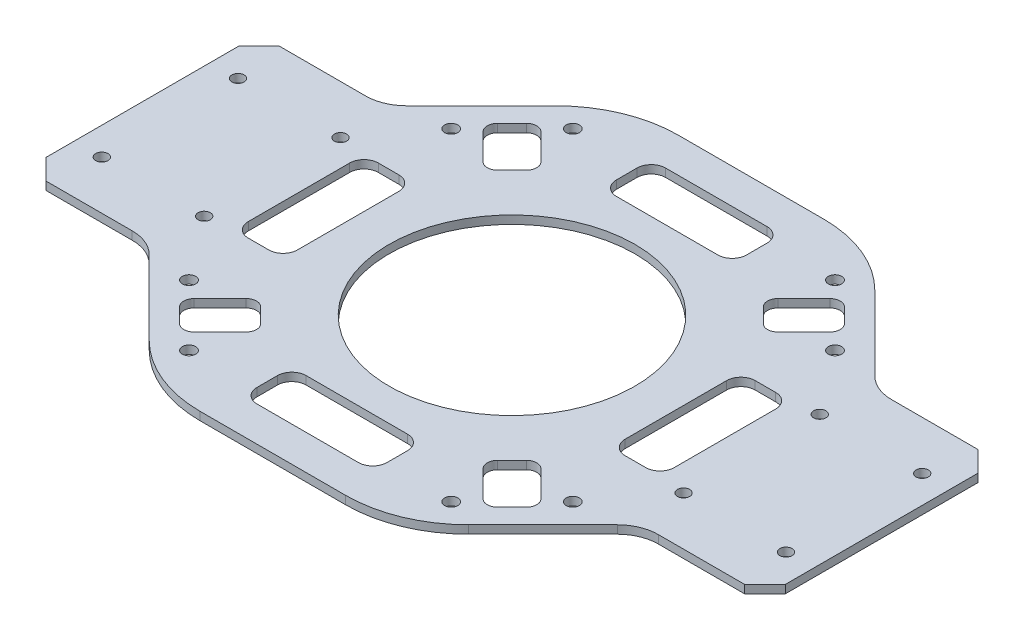
SolidWorks part; units mm, degrees
ref_plane "Front Plane" through (0, 0, 0) normal (0, 0, 1) x (1, 0, 0)
ref_plane "Top Plane" through (0, 0, 0) normal (0, 1, 0) x (1, 0, 0)
ref_plane "Right Plane" through (0, 0, 0) normal (1, 0, 0) x (0, 0, -1)
ref_plane "Plane1" through (0, 3.76, 0) normal (0, 1, 0) x (1, 0, 0)
sketch "Sketch1" plane through (0, 3.76, 0) normal (0, 1, 0) x (1, 0, 0)
  line L0 (-15.875, -46.375) -> (-15.875, -41.375)
  line L1 (-12.375, -37.875) -> (12.375, -37.875)
  line L2 (15.875, -41.375) -> (15.875, -46.375)
  line L3 (12.375, -49.875) -> (-12.375, -49.875)
  line L4 (15.875, 46.375) -> (15.875, 41.375)
  line L5 (12.375, 37.875) -> (-12.375, 37.875)
  line L6 (-15.875, 41.375) -> (-15.875, 46.375)
  line L7 (-12.375, 49.875) -> (12.375, 49.875)
  line L8 (-43.5, -15.875) -> (-48.5, -15.875)
  line L9 (-52, -12.375) -> (-52, 12.375)
  line L10 (-48.5, 15.875) -> (-43.5, 15.875)
  line L11 (-40, 12.375) -> (-40, -12.375)
  line L12 (-32.4385, -28.903) -> (-28.903, -32.4385)
  line L13 (-28.903, -35.9741) -> (-35.267, -42.338)
  line L14 (-38.8025, -42.338) -> (-42.338, -38.8025)
  line L15 (-42.338, -35.267) -> (-35.9741, -28.903)
  line L16 (32.4385, 28.903) -> (28.903, 32.4385)
  line L17 (28.903, 35.9741) -> (35.267, 42.338)
  line L18 (38.8025, 42.338) -> (42.338, 38.8025)
  line L19 (42.338, 35.267) -> (35.9741, 28.903)
  line L20 (28.903, -32.4385) -> (32.4385, -28.903)
  line L21 (35.9741, -28.903) -> (42.338, -35.267)
  line L22 (42.338, -38.8025) -> (38.8025, -42.338)
  line L23 (35.267, -42.338) -> (28.903, -35.9741)
  line L24 (-28.903, 32.4385) -> (-32.4385, 28.903)
  line L25 (-35.9741, 28.903) -> (-42.338, 35.267)
  line L26 (-42.338, 38.8025) -> (-38.8025, 42.338)
  line L27 (-35.267, 42.338) -> (-28.903, 35.9741)
  line L28 (43.5, 15.875) -> (48.5, 15.875)
  line L29 (52, 12.375) -> (52, -12.375)
  line L30 (48.5, -15.875) -> (43.5, -15.875)
  line L31 (40, -12.375) -> (40, 12.375)
  line L32 (-17.7637, -58.375) -> (17.7637, -58.375)
  line L33 (38.9769, -49.5882) -> (57.1362, -31.4289)
  line L34 (64.2073, -28.5) -> (85.25, -28.5)
  line L35 (85.25, -28.5) -> (90.25, -23.5)
  line L36 (90.25, -23.5) -> (90.25, 23.5)
  line L37 (90.25, 23.5) -> (85.25, 28.5)
  line L38 (85.25, 28.5) -> (64.2073, 28.5)
  line L39 (57.1362, 31.4289) -> (38.9769, 49.5882)
  line L40 (17.7637, 58.375) -> (-17.7637, 58.375)
  line L41 (-38.9769, 49.5882) -> (-57.1362, 31.4289)
  line L42 (-64.2073, 28.5) -> (-85.25, 28.5)
  line L43 (-85.25, 28.5) -> (-90.25, 23.5)
  line L44 (-90.25, 23.5) -> (-90.25, -23.5)
  line L45 (-90.25, -23.5) -> (-85.25, -28.5)
  line L46 (-85.25, -28.5) -> (-64.2073, -28.5)
  line L47 (-57.1362, -31.4289) -> (-38.9769, -49.5882)
  arc A0 (-12.375, -49.875) -> (-15.875, -46.375) centre (-12.375, -46.375) cw
  arc A1 (-15.875, -41.375) -> (-12.375, -37.875) centre (-12.375, -41.375) cw
  arc A2 (12.375, -37.875) -> (15.875, -41.375) centre (12.375, -41.375) cw
  arc A3 (15.875, -46.375) -> (12.375, -49.875) centre (12.375, -46.375) cw
  circle A4 centre (31.9966, 46.8458) radius 1.625
  arc A5 (15.875, 41.375) -> (12.375, 37.875) centre (12.375, 41.375) cw
  arc A6 (-12.375, 37.875) -> (-15.875, 41.375) centre (-12.375, 41.375) cw
  arc A7 (-15.875, 46.375) -> (-12.375, 49.875) centre (-12.375, 46.375) cw
  arc A8 (12.375, 49.875) -> (15.875, 46.375) centre (12.375, 46.375) cw
  circle A9 centre (31.9966, -46.8458) radius 1.625
  circle A10 centre (-31.9966, 46.8458) radius 1.625
  circle A11 centre (58.5, -16.625) radius 1.5
  circle A12 centre (-58.5, 16.625) radius 1.5
  arc A13 (-40, -12.375) -> (-43.5, -15.875) centre (-43.5, -12.375) cw
  arc A14 (-48.5, -15.875) -> (-52, -12.375) centre (-48.5, -12.375) cw
  arc A15 (-52, 12.375) -> (-48.5, 15.875) centre (-48.5, 12.375) cw
  arc A16 (-43.5, 15.875) -> (-40, 12.375) centre (-43.5, 12.375) cw
  arc A17 (-35.9741, -28.903) -> (-32.4385, -28.903) centre (-34.2063, -30.6708) cw
  arc A18 (-28.903, -32.4385) -> (-28.903, -35.9741) centre (-30.6708, -34.2063) cw
  arc A19 (-35.267, -42.338) -> (-38.8025, -42.338) centre (-37.0347, -40.5703) cw
  arc A20 (-42.338, -38.8025) -> (-42.338, -35.267) centre (-40.5703, -37.0347) cw
  arc A21 (35.9741, 28.903) -> (32.4385, 28.903) centre (34.2063, 30.6708) cw
  arc A22 (28.903, 32.4385) -> (28.903, 35.9741) centre (30.6708, 34.2063) cw
  arc A23 (35.267, 42.338) -> (38.8025, 42.338) centre (37.0347, 40.5703) cw
  arc A24 (42.338, 38.8025) -> (42.338, 35.267) centre (40.5703, 37.0347) cw
  arc A25 (28.903, -35.9741) -> (28.903, -32.4385) centre (30.6708, -34.2063) cw
  arc A26 (32.4385, -28.903) -> (35.9741, -28.903) centre (34.2063, -30.6708) cw
  arc A27 (42.338, -35.267) -> (42.338, -38.8025) centre (40.5703, -37.0347) cw
  arc A28 (38.8025, -42.338) -> (35.267, -42.338) centre (37.0347, -40.5703) cw
  arc A29 (-28.903, 35.9741) -> (-28.903, 32.4385) centre (-30.6708, 34.2063) cw
  arc A30 (-32.4385, 28.903) -> (-35.9741, 28.903) centre (-34.2063, 30.6708) cw
  arc A31 (-42.338, 35.267) -> (-42.338, 38.8025) centre (-40.5703, 37.0347) cw
  arc A32 (-38.8025, 42.338) -> (-35.267, 42.338) centre (-37.0347, 40.5703) cw
  arc A33 (40, 12.375) -> (43.5, 15.875) centre (43.5, 12.375) cw
  arc A34 (48.5, 15.875) -> (52, 12.375) centre (48.5, 12.375) cw
  arc A35 (52, -12.375) -> (48.5, -15.875) centre (48.5, -12.375) cw
  arc A36 (43.5, -15.875) -> (40, -12.375) centre (43.5, -12.375) cw
  circle A37 centre (-58.5, -16.625) radius 1.5
  circle A38 centre (58.5, 16.625) radius 1.5
  circle A39 centre (-83.5, 16.625) radius 1.5
  circle A40 centre (-83.5, -16.625) radius 1.5
  circle A41 centre (83.5, -16.625) radius 1.5
  circle A42 centre (83.5, 16.625) radius 1.5
  circle A43 centre (0, 0) radius 30
  circle A44 centre (46.8458, 31.9966) radius 1.625
  circle A45 centre (46.8458, -31.9966) radius 1.625
  circle A46 centre (-46.8458, 31.9966) radius 1.625
  circle A47 centre (-46.8458, -31.9966) radius 1.625
  circle A48 centre (-31.9966, -46.8458) radius 1.625
  arc A49 (-38.9769, -49.5882) -> (-17.7637, -58.375) centre (-17.7637, -28.375) ccw
  arc A50 (17.7637, -58.375) -> (38.9769, -49.5882) centre (17.7637, -28.375) ccw
  arc A51 (57.1362, -31.4289) -> (64.2073, -28.5) centre (64.2073, -38.5) cw
  arc A52 (64.2073, 28.5) -> (57.1362, 31.4289) centre (64.2073, 38.5) cw
  arc A53 (38.9769, 49.5882) -> (17.7637, 58.375) centre (17.7637, 28.375) ccw
  arc A54 (-17.7637, 58.375) -> (-38.9769, 49.5882) centre (-17.7637, 28.375) ccw
  arc A55 (-57.1362, 31.4289) -> (-64.2073, 28.5) centre (-64.2073, 38.5) cw
  arc A56 (-64.2073, -28.5) -> (-57.1362, -31.4289) centre (-64.2073, -38.5) cw
extrude "Boss-Extrude1" add sketch "Sketch1" against normal blind 2
